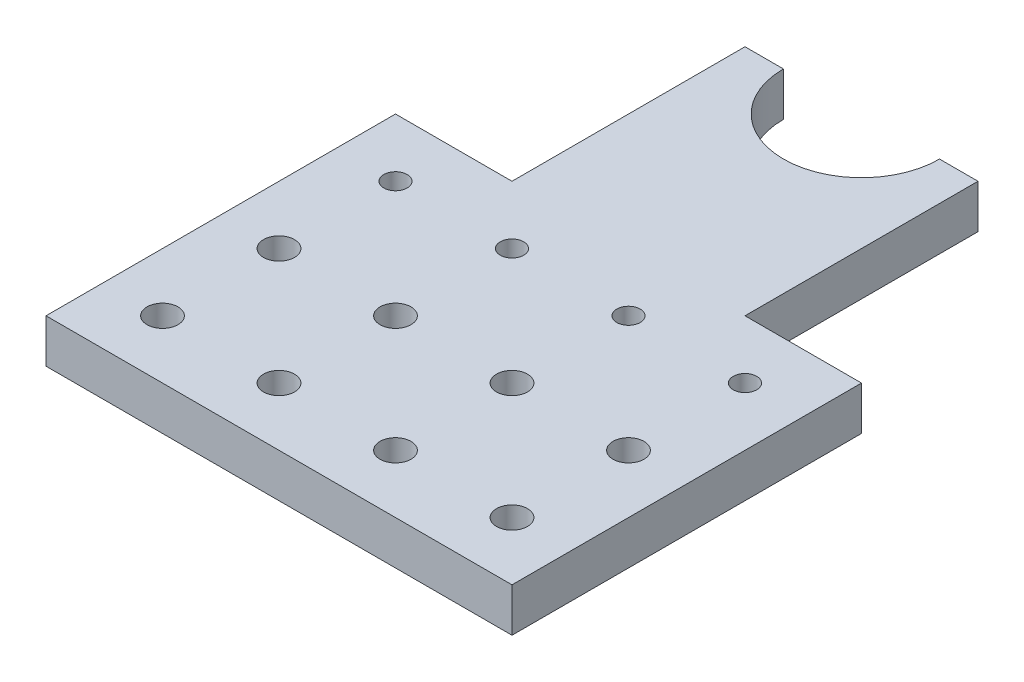
SolidWorks part; units mm, degrees
ref_plane "Front Plane" through (0, 0, 0) normal (0, 0, 1) x (1, 0, 0)
ref_plane "Top Plane" through (0, 0, 0) normal (0, 1, 0) x (1, 0, 0)
ref_plane "Right Plane" through (0, 0, 0) normal (1, 0, 0) x (0, 0, -1)
sketch "Sketch1" plane through (0, 0, 0) normal (0, 1, 0) x (1, 0, 0)
  line L1 (0, 0) -> (101.6, 0)
  line L2 (0, 0) -> (0, 127)
  line L3 (0, 127) -> (101.6, 127)
  line L4 (101.6, 0) -> (101.6, 127)
extrude "Boss-Extrude1" add sketch "Sketch1" along normal blind 9.525
sketch "Sketch2" plane through (0, 9.525, 0) normal (0, 1, 0) x (1, 0, 0)
  line L0 (101.6, 127) -> (0, 127) construction
  circle A0 centre (50.8, 127) radius 17.018
extrude "Cut-Extrude1" cut sketch "Sketch2" against normal through all
hole_wizard "1/4 Clearance Hole1" positions "Sketch4" profile "Sketch3" hole size "1/4" standard "Ansi Inch" end condition through all
sketch "Sketch4" plane through (0, 9.525, 0) normal (0, 1, 0) x (-1, 0, 0)
  point P0 (-12.7, -12.7)
sketch "Sketch3" plane through (12.7, 9.525, -12.7) normal (1, 0, 0) x (0, 0, 1)
  line L0 (0, 0) -> (0, 9.525)
  line L1 (0, 9.525) -> (3.3782, 9.525)
  line L2 (3.3782, 9.525) -> (3.3782, 0)
  line L5 (3.3782, 0) -> (0, 0)
  line L11 (0, -6.35) -> (0, 107.95) construction
  dimension "Thru Hole Dia." = 6.7564
  dimension "Thru Hole Depth" = 9.525
pattern_linear "LPattern1" count 2 spacing 25.4 along (0, 0, -1) count 4 spacing 25.4 along (1, 0, 0) of "1/4 Clearance Hole1"
hole_wizard "Tap Drill for 1/4-20 Tap1" positions "Sketch6" profile "Sketch5" hole size "1/4-20" standard "Ansi Inch" end condition through all
sketch "Sketch6" plane through (0, 9.525, 0) normal (0, 1, 0) x (-1, 0, 0)
  point P0 (-12.7, -63.5)
sketch "Sketch5" plane through (12.7, 9.525, -63.5) normal (1, 0, 0) x (0, 0, 1)
  line L0 (0, 0) -> (0, 9.525)
  line L1 (0, 9.525) -> (2.5527, 9.525)
  line L2 (2.5527, 9.525) -> (2.5527, 0)
  line L5 (2.5527, 0) -> (0, 0)
  line L11 (0, -6.35) -> (0, 107.95) construction
  dimension "Thru Hole Dia." = 5.1054
  dimension "Thru Hole Depth" = 9.525
pattern_linear "LPattern2" count 4 spacing 25.4 along (1, 0, 0) of "Tap Drill for 1/4-20 Tap1"
sketch "Sketch7" plane through (0, 9.525, 0) normal (0, 1, 0) x (1, 0, 0)
  line L1 (0, 127) -> (25.4, 127)
  line L2 (0, 127) -> (0, 76.2)
  line L3 (0, 76.2) -> (25.4, 76.2)
  line L4 (25.4, 127) -> (25.4, 76.2)
  line L5 (101.6, 127) -> (76.2, 127)
  line L6 (101.6, 127) -> (101.6, 76.2)
  line L7 (101.6, 76.2) -> (76.2, 76.2)
  line L8 (76.2, 127) -> (76.2, 76.2)
extrude "Cut-Extrude2" cut sketch "Sketch7" against normal through all
hole_wizard "#8-32 Tapped Hole1" positions "Sketch9" profile "Sketch8" tap size "#8-32" standard "Ansi Inch"
sketch "Sketch9" plane through (0, 0, -127) normal (0, 0, -1) x (-1, 0, 0)
  point P0 (-29.6545, 4.7625)
sketch "Sketch8" plane through (29.6545, 4.7625, -127) normal (1, 0, 0) x (0, 1, 0)
  line L0 (0, 0) -> (0, 11.7058)
  line L1 (0, 11.7058) -> (1.7272, 10.668)
  line L2 (1.7272, 10.668) -> (1.7272, 0)
  line L5 (1.7272, 0) -> (0, 0)
  line L10 (0, 11.7058) -> (-1.7272, 10.668) construction
  line L11 (0, -6.35) -> (0, 107.95) construction
  dimension "Tap Drill Dia." = 3.4544
  dimension "Tap Drill Depth" = 10.668
  dimension "Drill Angle" = 118
cosmetic thread "Hole Thread1" parameters "D1"=8.382, "D2"=4.1656
pattern_linear "LPattern3" count 2 spacing 42.291 along (1, 0, 0) of "#8-32 Tapped Hole1"
